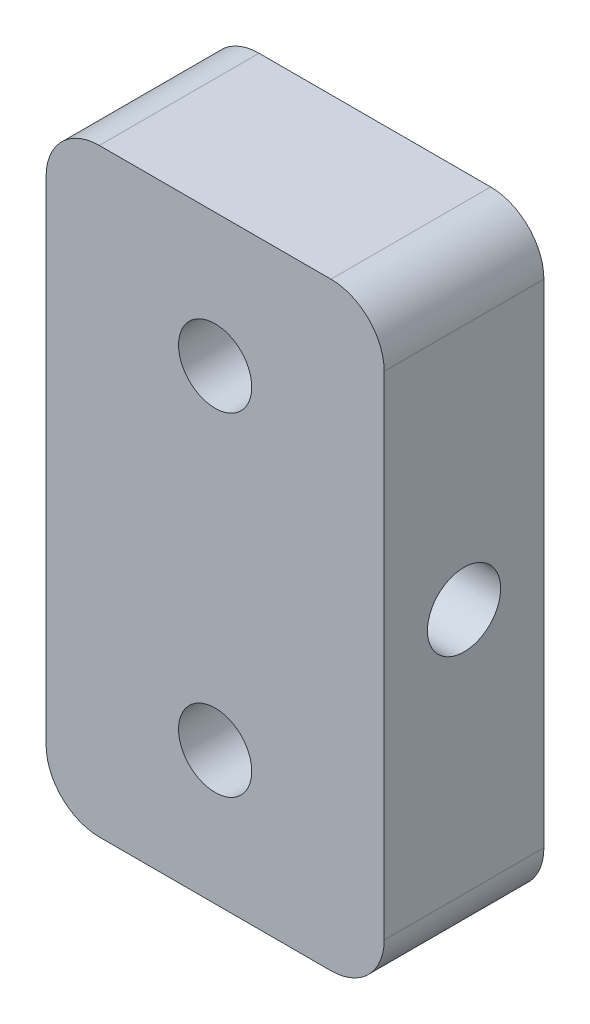
SolidWorks part; units mm, degrees
material "1060 Alloy"
ref_plane "Front Plane" through (0, 0, 0) normal (0, 0, 1) x (1, 0, 0)
ref_plane "Top Plane" through (0, 0, 0) normal (0, 1, 0) x (1, 0, 0)
ref_plane "Right Plane" through (0, 0, 0) normal (1, 0, 0) x (0, 0, -1)
sketch "Sketch1" plane through (0, 0, 0) normal (0, 0, 1) x (1, 0, 0)
  line L1 (12.7, -22.5) -> (-12.7, -22.5)
  line L2 (12.7, -22.5) -> (12.7, 22.5)
  line L3 (12.7, 22.5) -> (-12.7, 22.5)
  line L4 (-12.7, -22.5) -> (-12.7, 22.5)
  line L5 (12.7, -22.5) -> (-12.7, 22.5) construction
  line L6 (12.7, 22.5) -> (-12.7, -22.5) construction
  point P0 (0, 0)
  dimension "D1" = 45
  dimension "D2" = 25.4
extrude "Boss-Extrude1" add sketch "Sketch1" along normal mid plane 12
fillet "Fillet1" radius 4 4 edges at (-12.7, -22.5, 0) (12.7, -22.5, 0) (12.7, 22.5, 0) (-12.7, 22.5, 0)
hole_wizard "M5 Clearance Hole1" positions "Sketch3" profile "Sketch4" hole size "M5" standard "AS" end condition through all
sketch "Sketch3" plane through (-12.7, 0, 0) normal (-1, 0, 0) x (0, 0, 1)
  point P0 (0, 0)
sketch "Sketch4" plane through (-12.7, 0, 0) normal (0, 1, 0) x (0, 0, 1)
  line L0 (0, 0) -> (0, 25.4)
  line L1 (0, 25.4) -> (2.75, 25.4)
  line L2 (2.75, 25.4) -> (2.75, 0)
  line L5 (2.75, 0) -> (0, 0)
  line L11 (0, -6.35) -> (0, 107.95) construction
  dimension "Thru Hole Dia." = 5.5
  dimension "Thru Hole Depth" = 25.4
sketch "Sketch5" plane through (0, 0, -6) normal (0, 0, -1) x (-1, 0, 0)
  line L0 (0, -12.5) -> (0, 12.5) construction
  point P4 (0, 0)
  dimension "D1" = 25
hole_wizard "M5 Clearance Hole2" positions "Sketch6" profile "Sketch7" hole size "M5" standard "AS" end condition through all
sketch "Sketch6" plane through (0, 0, -6) normal (0, 0, -1) x (-1, 0, 0)
  point P0 (0, 12.5)
  point P3 (0, -12.5)
sketch "Sketch7" plane through (0, 12.5, -6) normal (1, 0, 0) x (0, 1, 0)
  line L0 (0, 0) -> (0, 12)
  line L1 (0, 12) -> (2.75, 12)
  line L2 (2.75, 12) -> (2.75, 0)
  line L5 (2.75, 0) -> (0, 0)
  line L11 (0, -6.35) -> (0, 107.95) construction
  dimension "Thru Hole Dia." = 5.5
  dimension "Thru Hole Depth" = 12
